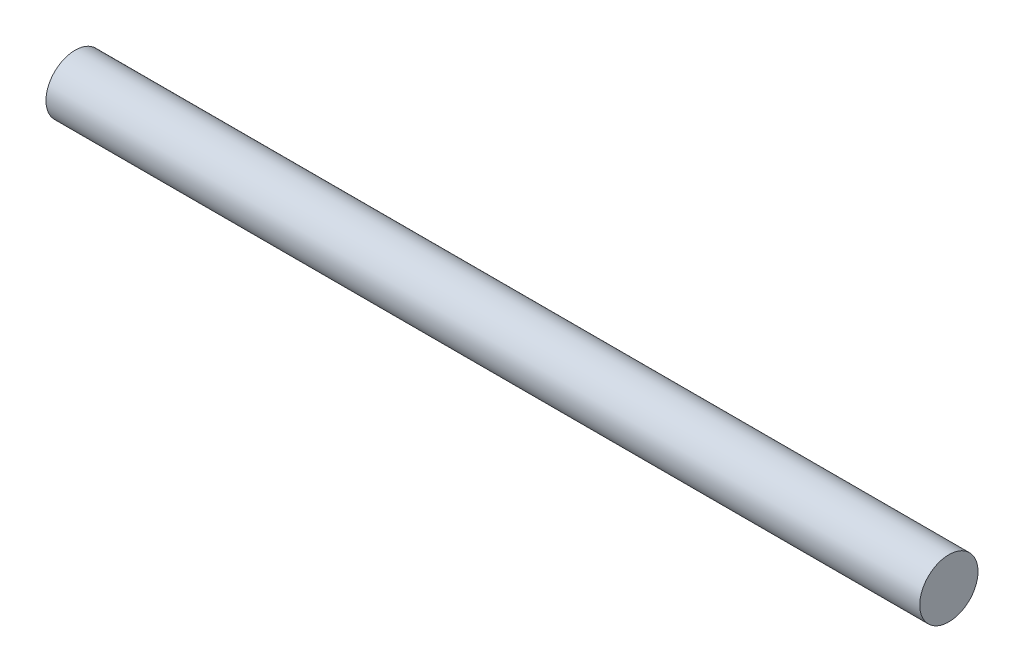
SolidWorks part; units mm, degrees
ref_plane "前视基准面" through (0, 0, 0) normal (0, 0, 1) x (1, 0, 0)
ref_plane "上视基准面" through (0, 0, 0) normal (0, 1, 0) x (1, 0, 0)
ref_plane "右视基准面" through (0, 0, 0) normal (1, 0, 0) x (0, 0, -1)
sketch "草图1" plane through (0, 0, 0) normal (1, 0, 0) x (0, 0, -1)
  circle A0 centre (0, 0) radius 5
  dimension "D1" = 10
extrude "凸台-拉伸1" add sketch "草图1" along normal blind 150
